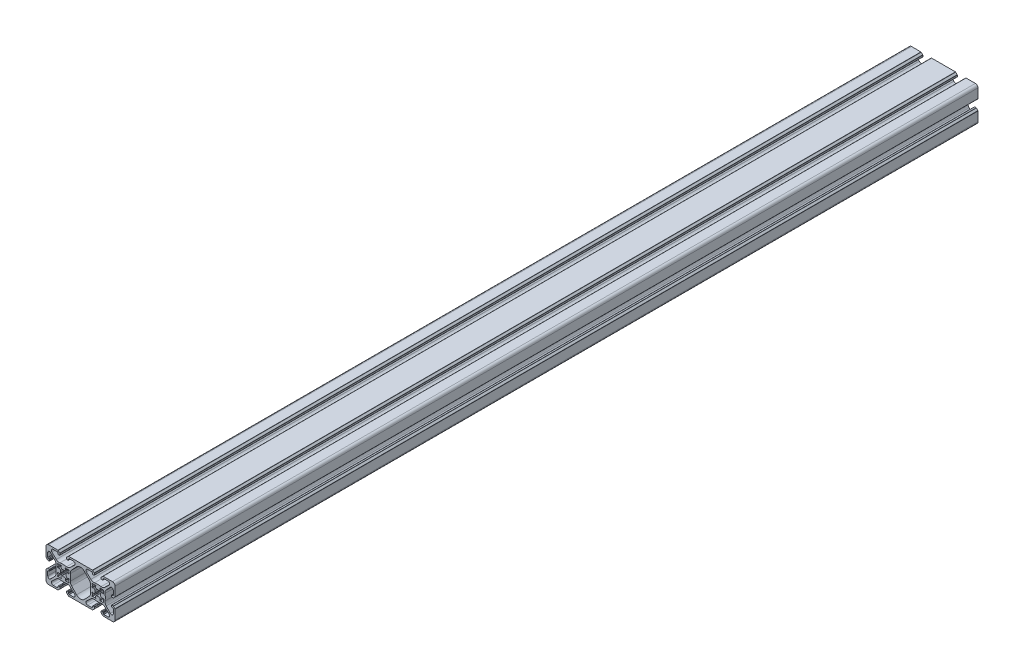
SolidWorks part; units mm, degrees
ref_plane "Front Plane" through (0, 0, 0) normal (0, 0, 1) x (1, 0, 0)
ref_plane "Top Plane" through (0, 0, 0) normal (0, 1, 0) x (1, 0, 0)
ref_plane "Right Plane" through (0, 0, 0) normal (1, 0, 0) x (0, 0, -1)
sketch "Model" plane through (0, 0, 0) normal (0, 0, 1) x (1, 0, 0)
  line L0 (1975.9541, 1652.1362) -> (1976.9672, 1652.4076)
  line L1 (1973.0632, 1648.5036) -> (1973.3346, 1649.5167)
  line L2 (1968.2453, 1649.5167) -> (1968.5168, 1648.5036)
  line L3 (1964.6128, 1652.4076) -> (1965.6258, 1652.1362)
  line L4 (1965.6258, 1657.2255) -> (1964.6128, 1656.954)
  line L5 (1968.5168, 1660.858) -> (1968.2453, 1659.845)
  line L6 (1973.3346, 1659.845) -> (1973.0632, 1660.858)
  line L7 (1976.9672, 1656.954) -> (1975.9541, 1657.2255)
  line L9 (2005.6258, 1652.1362) -> (2004.6128, 1652.4076)
  line L10 (2008.5168, 1648.5036) -> (2008.2453, 1649.5167)
  line L11 (2013.3346, 1649.5167) -> (2013.0632, 1648.5036)
  line L12 (2016.9672, 1652.4076) -> (2015.9541, 1652.1362)
  line L13 (2015.9541, 1657.2255) -> (2016.9672, 1656.954)
  line L14 (2013.0632, 1660.858) -> (2013.3346, 1659.845)
  line L15 (2008.2453, 1659.845) -> (2008.5168, 1660.858)
  line L16 (2004.6128, 1656.954) -> (2005.6258, 1657.2255)
  line L17 (1980.5086, 1646.6346) -> (1986.1807, 1640.6604)
  line L18 (1995.3992, 1640.6604) -> (2001.0713, 1646.6346)
  line L19 (2001.0713, 1662.727) -> (1995.3992, 1668.7012)
  line L20 (1986.1807, 1668.7012) -> (1980.5086, 1662.727)
  line L22 (2004.5828, 1674.6808) -> (1976.9971, 1674.6808)
  line L23 (1976.6435, 1674.5344) -> (1974.9364, 1672.8273)
  line L24 (1974.79, 1672.4737) -> (1974.79, 1670.8808)
  line L25 (1975.29, 1670.3808) -> (1976.29, 1670.3808)
  line L26 (1976.79, 1670.8808) -> (1976.79, 1671.7281)
  line L27 (1976.8778, 1671.9403) -> (1977.5305, 1672.593)
  line L28 (1977.7426, 1672.6808) -> (1982.5473, 1672.6808)
  line L29 (1983.9244, 1669.2304) -> (1978.8362, 1664.3995)
  line L30 (1962.7437, 1664.3995) -> (1957.6555, 1669.2304)
  line L31 (1959.0326, 1672.6808) -> (1963.8373, 1672.6808)
  line L32 (1964.0494, 1672.593) -> (1964.7021, 1671.9403)
  line L33 (1964.79, 1671.7281) -> (1964.79, 1670.8808)
  line L34 (1965.29, 1670.3808) -> (1966.29, 1670.3808)
  line L35 (1966.79, 1670.8808) -> (1966.79, 1672.4737)
  line L36 (1966.6435, 1672.8273) -> (1964.9364, 1674.5344)
  line L37 (1964.5828, 1674.6808) -> (1953.79, 1674.6808)
  line L38 (1950.79, 1671.6808) -> (1950.79, 1660.8879)
  line L39 (1950.9364, 1660.5344) -> (1952.6435, 1658.8273)
  line L40 (1952.9971, 1658.6808) -> (1954.59, 1658.6808)
  line L41 (1955.09, 1659.1808) -> (1955.09, 1660.1808)
  line L42 (1954.59, 1660.6808) -> (1953.7426, 1660.6808)
  line L43 (1953.5305, 1660.7687) -> (1952.8778, 1661.4214)
  line L44 (1952.79, 1661.6335) -> (1952.79, 1666.4382)
  line L45 (1956.2404, 1667.8153) -> (1961.0713, 1662.727)
  line L46 (1961.0713, 1646.6346) -> (1956.2404, 1641.5464)
  line L47 (1952.79, 1642.9235) -> (1952.79, 1647.7281)
  line L48 (1952.8778, 1647.9403) -> (1953.5305, 1648.593)
  line L49 (1953.7426, 1648.6808) -> (1954.59, 1648.6808)
  line L50 (1955.09, 1649.1808) -> (1955.09, 1650.1808)
  line L51 (1954.59, 1650.6808) -> (1952.9971, 1650.6808)
  line L52 (1952.6435, 1650.5344) -> (1950.9364, 1648.8273)
  line L53 (1950.79, 1648.4737) -> (1950.79, 1637.6808)
  line L54 (1953.79, 1634.6808) -> (1964.5828, 1634.6808)
  line L55 (1964.9364, 1634.8273) -> (1966.6435, 1636.5344)
  line L56 (1966.79, 1636.8879) -> (1966.79, 1638.4808)
  line L57 (1966.29, 1638.9808) -> (1965.29, 1638.9808)
  line L58 (1964.79, 1638.4808) -> (1964.79, 1637.6335)
  line L59 (1964.7021, 1637.4214) -> (1964.0494, 1636.7687)
  line L60 (1963.8373, 1636.6808) -> (1959.0326, 1636.6808)
  line L61 (1957.6555, 1640.1312) -> (1962.7437, 1644.9622)
  line L62 (1978.8362, 1644.9622) -> (1983.9244, 1640.1312)
  line L63 (1982.5473, 1636.6808) -> (1977.7426, 1636.6808)
  line L64 (1977.5305, 1636.7687) -> (1976.8778, 1637.4214)
  line L65 (1976.79, 1637.6335) -> (1976.79, 1638.4808)
  line L66 (1976.29, 1638.9808) -> (1975.29, 1638.9808)
  line L67 (1974.79, 1638.4808) -> (1974.79, 1636.8879)
  line L68 (1974.9364, 1636.5344) -> (1976.6435, 1634.8273)
  line L69 (1976.9971, 1634.6808) -> (2004.5828, 1634.6808)
  line L70 (2004.9364, 1634.8273) -> (2006.6435, 1636.5344)
  line L71 (2006.79, 1636.8879) -> (2006.79, 1638.4808)
  line L72 (2006.29, 1638.9808) -> (2005.29, 1638.9808)
  line L73 (2004.79, 1638.4808) -> (2004.79, 1637.6335)
  line L74 (2004.7021, 1637.4214) -> (2004.0494, 1636.7687)
  line L75 (2003.8373, 1636.6808) -> (1999.0326, 1636.6808)
  line L76 (1997.6555, 1640.1312) -> (2002.7437, 1644.9622)
  line L77 (2018.8362, 1644.9622) -> (2023.9244, 1640.1312)
  line L78 (2022.5473, 1636.6808) -> (2017.7426, 1636.6808)
  line L79 (2017.5305, 1636.7687) -> (2016.8778, 1637.4214)
  line L80 (2016.79, 1637.6335) -> (2016.79, 1638.4808)
  line L81 (2016.29, 1638.9808) -> (2015.29, 1638.9808)
  line L82 (2014.79, 1638.4808) -> (2014.79, 1636.8879)
  line L83 (2014.9364, 1636.5344) -> (2016.6435, 1634.8273)
  line L84 (2016.9971, 1634.6808) -> (2027.79, 1634.6808)
  line L85 (2030.79, 1637.6808) -> (2030.79, 1648.4737)
  line L86 (2030.6435, 1648.8273) -> (2028.9364, 1650.5344)
  line L87 (2028.5828, 1650.6808) -> (2026.99, 1650.6808)
  line L88 (2026.49, 1650.1808) -> (2026.49, 1649.1808)
  line L89 (2026.99, 1648.6808) -> (2027.8373, 1648.6808)
  line L90 (2028.0494, 1648.593) -> (2028.7021, 1647.9403)
  line L91 (2028.79, 1647.7281) -> (2028.79, 1642.9235)
  line L92 (2025.3395, 1641.5464) -> (2020.5086, 1646.6346)
  line L93 (2020.5086, 1662.727) -> (2025.3395, 1667.8153)
  line L94 (2028.79, 1666.4382) -> (2028.79, 1661.6335)
  line L95 (2028.7021, 1661.4214) -> (2028.0494, 1660.7687)
  line L96 (2027.8373, 1660.6808) -> (2026.99, 1660.6808)
  line L97 (2026.49, 1660.1808) -> (2026.49, 1659.1808)
  line L98 (2026.99, 1658.6808) -> (2028.5828, 1658.6808)
  line L99 (2028.9364, 1658.8273) -> (2030.6435, 1660.5344)
  line L100 (2030.79, 1660.8879) -> (2030.79, 1671.6808)
  line L101 (2027.79, 1674.6808) -> (2016.9971, 1674.6808)
  line L102 (2016.6435, 1674.5344) -> (2014.9364, 1672.8273)
  line L103 (2014.79, 1672.4737) -> (2014.79, 1670.8808)
  line L104 (2015.29, 1670.3808) -> (2016.29, 1670.3808)
  line L105 (2016.79, 1670.8808) -> (2016.79, 1671.7281)
  line L106 (2016.8778, 1671.9403) -> (2017.5305, 1672.593)
  line L107 (2017.7426, 1672.6808) -> (2022.5473, 1672.6808)
  line L108 (2023.9244, 1669.2304) -> (2018.8362, 1664.3995)
  line L109 (2002.7437, 1664.3995) -> (1997.6555, 1669.2304)
  line L110 (1999.0326, 1672.6808) -> (2003.8373, 1672.6808)
  line L111 (2004.0494, 1672.593) -> (2004.7021, 1671.9403)
  line L112 (2004.79, 1671.7281) -> (2004.79, 1670.8808)
  line L113 (2005.29, 1670.3808) -> (2006.29, 1670.3808)
  line L114 (2006.79, 1670.8808) -> (2006.79, 1672.4737)
  line L115 (2006.6435, 1672.8273) -> (2004.9364, 1674.5344)
  arc A0 (1977.3429, 1652.084) -> (1976.9672, 1652.4076) centre (1977.0448, 1652.1178) ccw
  arc A1 (1977.215, 1651.1353) -> (1977.3429, 1652.084) centre (1954.49, 1654.6808) ccw
  arc A2 (1977.215, 1651.1353) -> (1977.3, 1648.529) centre (1984.1314, 1650.0562) ccw
  arc A3 (1976.9418, 1648.1708) -> (1977.3, 1648.529) centre (1977.0072, 1648.4635) ccw
  arc A4 (1976.9418, 1648.1708) -> (1974.3355, 1648.2557) centre (1975.4145, 1641.3394) ccw
  arc A5 (1973.3868, 1648.1279) -> (1974.3355, 1648.2557) centre (1970.79, 1670.9808) ccw
  arc A6 (1973.0632, 1648.5036) -> (1973.3868, 1648.1279) centre (1973.3529, 1648.426) ccw
  arc A7 (1973.3346, 1649.5167) -> (1971.5503, 1651.3669) centre (1971.8857, 1649.9049) ccw
  arc A8 (1970.0296, 1651.3669) -> (1971.5503, 1651.3669) centre (1970.79, 1654.6808) ccw
  arc A9 (1970.0296, 1651.3669) -> (1968.2453, 1649.5167) centre (1969.6942, 1649.9049) ccw
  arc A10 (1968.1931, 1648.1279) -> (1968.5168, 1648.5036) centre (1968.227, 1648.426) ccw
  arc A11 (1967.2444, 1648.2557) -> (1968.1931, 1648.1279) centre (1970.79, 1670.9808) ccw
  arc A12 (1967.2444, 1648.2557) -> (1964.6381, 1648.1708) centre (1966.1654, 1641.3394) ccw
  arc A13 (1964.2799, 1648.529) -> (1964.6381, 1648.1708) centre (1964.5727, 1648.4635) ccw
  arc A14 (1964.2799, 1648.529) -> (1964.3649, 1651.1353) centre (1957.4485, 1650.0562) ccw
  arc A15 (1964.237, 1652.084) -> (1964.3649, 1651.1353) centre (1987.09, 1654.6808) ccw
  arc A16 (1964.6128, 1652.4076) -> (1964.237, 1652.084) centre (1964.5351, 1652.1178) ccw
  arc A17 (1965.6258, 1652.1362) -> (1967.4761, 1653.9205) centre (1966.014, 1653.5851) ccw
  arc A18 (1967.4761, 1655.4411) -> (1967.4761, 1653.9205) centre (1970.79, 1654.6808) ccw
  arc A19 (1967.4761, 1655.4411) -> (1965.6258, 1657.2255) centre (1966.014, 1655.7766) ccw
  arc A20 (1964.237, 1657.2777) -> (1964.6128, 1656.954) centre (1964.5351, 1657.2438) ccw
  arc A21 (1964.3649, 1658.2263) -> (1964.237, 1657.2777) centre (1987.09, 1654.6808) ccw
  arc A22 (1964.3649, 1658.2263) -> (1964.2799, 1660.8326) centre (1957.4485, 1659.3054) ccw
  arc A23 (1964.6381, 1661.1909) -> (1964.2799, 1660.8326) centre (1964.5727, 1660.8981) ccw
  arc A24 (1964.6381, 1661.1909) -> (1967.2444, 1661.1059) centre (1966.1654, 1668.0222) ccw
  arc A25 (1968.1931, 1661.2338) -> (1967.2444, 1661.1059) centre (1970.79, 1638.3808) ccw
  arc A26 (1968.5168, 1660.858) -> (1968.1931, 1661.2338) centre (1968.227, 1660.9357) ccw
  arc A27 (1968.2453, 1659.845) -> (1970.0296, 1657.9947) centre (1969.6942, 1659.4567) ccw
  arc A28 (1971.5503, 1657.9947) -> (1970.0296, 1657.9947) centre (1970.79, 1654.6808) ccw
  arc A29 (1971.5503, 1657.9947) -> (1973.3346, 1659.845) centre (1971.8857, 1659.4567) ccw
  arc A30 (1973.3868, 1661.2338) -> (1973.0632, 1660.858) centre (1973.3529, 1660.9357) ccw
  arc A31 (1974.3355, 1661.1059) -> (1973.3868, 1661.2338) centre (1970.79, 1638.3808) ccw
  arc A32 (1974.3355, 1661.1059) -> (1976.9418, 1661.1909) centre (1975.4145, 1668.0222) ccw
  arc A33 (1977.3, 1660.8326) -> (1976.9418, 1661.1909) centre (1977.0072, 1660.8981) ccw
  arc A34 (1977.3, 1660.8326) -> (1977.215, 1658.2263) centre (1984.1314, 1659.3054) ccw
  arc A35 (1977.3429, 1657.2777) -> (1977.215, 1658.2263) centre (1954.49, 1654.6808) ccw
  arc A36 (1976.9672, 1656.954) -> (1977.3429, 1657.2777) centre (1977.0448, 1657.2438) ccw
  arc A37 (1975.9541, 1657.2255) -> (1974.1039, 1655.4411) centre (1975.5659, 1655.7766) ccw
  arc A38 (1974.1039, 1653.9205) -> (1974.1039, 1655.4411) centre (1970.79, 1654.6808) ccw
  arc A39 (1974.1039, 1653.9205) -> (1975.9541, 1652.1362) centre (1975.5659, 1653.5851) ccw
  arc A40 (2004.6128, 1652.4076) -> (2004.237, 1652.084) centre (2004.5351, 1652.1178) ccw
  arc A41 (2004.237, 1652.084) -> (2004.3649, 1651.1353) centre (2027.09, 1654.6808) ccw
  arc A42 (2004.2799, 1648.529) -> (2004.3649, 1651.1353) centre (1997.4485, 1650.0562) ccw
  arc A43 (2004.2799, 1648.529) -> (2004.6381, 1648.1708) centre (2004.5727, 1648.4635) ccw
  arc A44 (2007.2444, 1648.2557) -> (2004.6381, 1648.1708) centre (2006.1654, 1641.3394) ccw
  arc A45 (2007.2444, 1648.2557) -> (2008.1931, 1648.1279) centre (2010.79, 1670.9808) ccw
  arc A46 (2008.1931, 1648.1279) -> (2008.5168, 1648.5036) centre (2008.227, 1648.426) ccw
  arc A47 (2010.0296, 1651.3669) -> (2008.2453, 1649.5167) centre (2009.6942, 1649.9049) ccw
  arc A48 (2010.0296, 1651.3669) -> (2011.5503, 1651.3669) centre (2010.79, 1654.6808) ccw
  arc A49 (2013.3346, 1649.5167) -> (2011.5503, 1651.3669) centre (2011.8857, 1649.9049) ccw
  arc A50 (2013.0632, 1648.5036) -> (2013.3868, 1648.1279) centre (2013.3529, 1648.426) ccw
  arc A51 (2013.3868, 1648.1279) -> (2014.3355, 1648.2557) centre (2010.79, 1670.9808) ccw
  arc A52 (2016.9418, 1648.1708) -> (2014.3355, 1648.2557) centre (2015.4145, 1641.3394) ccw
  arc A53 (2016.9418, 1648.1708) -> (2017.3, 1648.529) centre (2017.0072, 1648.4635) ccw
  arc A54 (2017.215, 1651.1353) -> (2017.3, 1648.529) centre (2024.1314, 1650.0562) ccw
  arc A55 (2017.215, 1651.1353) -> (2017.3429, 1652.084) centre (1994.49, 1654.6808) ccw
  arc A56 (2017.3429, 1652.084) -> (2016.9672, 1652.4076) centre (2017.0448, 1652.1178) ccw
  arc A57 (2014.1039, 1653.9205) -> (2015.9541, 1652.1362) centre (2015.5659, 1653.5851) ccw
  arc A58 (2014.1039, 1653.9205) -> (2014.1039, 1655.4411) centre (2010.79, 1654.6808) ccw
  arc A59 (2015.9541, 1657.2255) -> (2014.1039, 1655.4411) centre (2015.5659, 1655.7766) ccw
  arc A60 (2016.9672, 1656.954) -> (2017.3429, 1657.2777) centre (2017.0448, 1657.2438) ccw
  arc A61 (2017.3429, 1657.2777) -> (2017.215, 1658.2263) centre (1994.49, 1654.6808) ccw
  arc A62 (2017.3, 1660.8326) -> (2017.215, 1658.2263) centre (2024.1314, 1659.3054) ccw
  arc A63 (2017.3, 1660.8326) -> (2016.9418, 1661.1909) centre (2017.0072, 1660.8981) ccw
  arc A64 (2014.3355, 1661.1059) -> (2016.9418, 1661.1909) centre (2015.4145, 1668.0222) ccw
  arc A65 (2014.3355, 1661.1059) -> (2013.3868, 1661.2338) centre (2010.79, 1638.3808) ccw
  arc A66 (2013.3868, 1661.2338) -> (2013.0632, 1660.858) centre (2013.3529, 1660.9357) ccw
  arc A67 (2011.5503, 1657.9947) -> (2013.3346, 1659.845) centre (2011.8857, 1659.4567) ccw
  arc A68 (2011.5503, 1657.9947) -> (2010.0296, 1657.9947) centre (2010.79, 1654.6808) ccw
  arc A69 (2008.2453, 1659.845) -> (2010.0296, 1657.9947) centre (2009.6942, 1659.4567) ccw
  arc A70 (2008.5168, 1660.858) -> (2008.1931, 1661.2338) centre (2008.227, 1660.9357) ccw
  arc A71 (2008.1931, 1661.2338) -> (2007.2444, 1661.1059) centre (2010.79, 1638.3808) ccw
  arc A72 (2004.6381, 1661.1909) -> (2007.2444, 1661.1059) centre (2006.1654, 1668.0222) ccw
  arc A73 (2004.6381, 1661.1909) -> (2004.2799, 1660.8326) centre (2004.5727, 1660.8981) ccw
  arc A74 (2004.3649, 1658.2263) -> (2004.2799, 1660.8326) centre (1997.4485, 1659.3054) ccw
  arc A75 (2004.3649, 1658.2263) -> (2004.237, 1657.2777) centre (2027.09, 1654.6808) ccw
  arc A76 (2004.237, 1657.2777) -> (2004.6128, 1656.954) centre (2004.5351, 1657.2438) ccw
  arc A77 (2007.4761, 1655.4411) -> (2005.6258, 1657.2255) centre (2006.014, 1655.7766) ccw
  arc A78 (2007.4761, 1655.4411) -> (2007.4761, 1653.9205) centre (2010.79, 1654.6808) ccw
  arc A79 (2005.6258, 1652.1362) -> (2007.4761, 1653.9205) centre (2006.014, 1653.5851) ccw
  arc A80 (1979.1939, 1650.8445) -> (1979.1939, 1658.5171) centre (1954.49, 1654.6808) ccw
  arc A81 (1979.1939, 1650.8445) -> (1980.5086, 1646.6346) centre (1984.1346, 1650.0773) ccw
  arc A82 (1986.1807, 1640.6604) -> (1995.3992, 1640.6604) centre (1990.79, 1645.0366) ccw
  arc A83 (2001.0713, 1646.6346) -> (2002.3861, 1650.8445) centre (1997.4453, 1650.0773) ccw
  arc A84 (2002.3861, 1658.5171) -> (2002.3861, 1650.8445) centre (2027.09, 1654.6808) ccw
  arc A85 (2002.3861, 1658.5171) -> (2001.0713, 1662.727) centre (1997.4453, 1659.2844) ccw
  arc A86 (1995.3992, 1668.7012) -> (1986.1807, 1668.7012) centre (1990.79, 1664.325) ccw
  arc A87 (1980.5086, 1662.727) -> (1979.1939, 1658.5171) centre (1984.1346, 1659.2844) ccw
  arc A88 (1976.9971, 1674.6808) -> (1976.6435, 1674.5344) centre (1976.9971, 1674.1808) ccw
  arc A89 (1974.9364, 1672.8273) -> (1974.79, 1672.4737) centre (1975.29, 1672.4737) ccw
  arc A90 (1974.79, 1670.8808) -> (1975.29, 1670.3808) centre (1975.29, 1670.8808) ccw
  arc A91 (1976.29, 1670.3808) -> (1976.79, 1670.8808) centre (1976.29, 1670.8808) ccw
  arc A92 (1976.8778, 1671.9403) -> (1976.79, 1671.7281) centre (1977.09, 1671.7281) ccw
  arc A93 (1977.7426, 1672.6808) -> (1977.5305, 1672.593) centre (1977.7426, 1672.3808) ccw
  arc A94 (1983.9244, 1669.2304) -> (1982.5473, 1672.6808) centre (1982.5473, 1670.6808) ccw
  arc A95 (1974.6262, 1663.0847) -> (1978.8362, 1664.3995) centre (1975.3935, 1668.0255) ccw
  arc A96 (1974.6262, 1663.0847) -> (1966.9537, 1663.0847) centre (1970.79, 1638.3808) ccw
  arc A97 (1962.7437, 1664.3995) -> (1966.9537, 1663.0847) centre (1966.1864, 1668.0255) ccw
  arc A98 (1959.0326, 1672.6808) -> (1957.6555, 1669.2304) centre (1959.0326, 1670.6808) ccw
  arc A99 (1964.0494, 1672.593) -> (1963.8373, 1672.6808) centre (1963.8373, 1672.3808) ccw
  arc A100 (1964.79, 1671.7281) -> (1964.7021, 1671.9403) centre (1964.49, 1671.7281) ccw
  arc A101 (1964.79, 1670.8808) -> (1965.29, 1670.3808) centre (1965.29, 1670.8808) ccw
  arc A102 (1966.29, 1670.3808) -> (1966.79, 1670.8808) centre (1966.29, 1670.8808) ccw
  arc A103 (1966.79, 1672.4737) -> (1966.6435, 1672.8273) centre (1966.29, 1672.4737) ccw
  arc A104 (1964.9364, 1674.5344) -> (1964.5828, 1674.6808) centre (1964.5828, 1674.1808) ccw
  arc A105 (1953.79, 1674.6808) -> (1950.79, 1671.6808) centre (1953.79, 1671.6808) ccw
  arc A106 (1950.79, 1660.8879) -> (1950.9364, 1660.5344) centre (1951.29, 1660.8879) ccw
  arc A107 (1952.6435, 1658.8273) -> (1952.9971, 1658.6808) centre (1952.9971, 1659.1808) ccw
  arc A108 (1954.59, 1658.6808) -> (1955.09, 1659.1808) centre (1954.59, 1659.1808) ccw
  arc A109 (1955.09, 1660.1808) -> (1954.59, 1660.6808) centre (1954.59, 1660.1808) ccw
  arc A110 (1953.5305, 1660.7687) -> (1953.7426, 1660.6808) centre (1953.7426, 1660.9808) ccw
  arc A111 (1952.79, 1661.6335) -> (1952.8778, 1661.4214) centre (1953.09, 1661.6335) ccw
  arc A112 (1956.2404, 1667.8153) -> (1952.79, 1666.4382) centre (1954.79, 1666.4382) ccw
  arc A113 (1962.3861, 1658.5171) -> (1961.0713, 1662.727) centre (1957.4453, 1659.2844) ccw
  arc A114 (1962.3861, 1658.5171) -> (1962.3861, 1650.8445) centre (1987.09, 1654.6808) ccw
  arc A115 (1961.0713, 1646.6346) -> (1962.3861, 1650.8445) centre (1957.4453, 1650.0773) ccw
  arc A116 (1952.79, 1642.9235) -> (1956.2404, 1641.5464) centre (1954.79, 1642.9235) ccw
  arc A117 (1952.8778, 1647.9403) -> (1952.79, 1647.7281) centre (1953.09, 1647.7281) ccw
  arc A118 (1953.7426, 1648.6808) -> (1953.5305, 1648.593) centre (1953.7426, 1648.3808) ccw
  arc A119 (1954.59, 1648.6808) -> (1955.09, 1649.1808) centre (1954.59, 1649.1808) ccw
  arc A120 (1955.09, 1650.1808) -> (1954.59, 1650.6808) centre (1954.59, 1650.1808) ccw
  arc A121 (1952.9971, 1650.6808) -> (1952.6435, 1650.5344) centre (1952.9971, 1650.1808) ccw
  arc A122 (1950.9364, 1648.8273) -> (1950.79, 1648.4737) centre (1951.29, 1648.4737) ccw
  arc A123 (1950.79, 1637.6808) -> (1953.79, 1634.6808) centre (1953.79, 1637.6808) ccw
  arc A124 (1964.5828, 1634.6808) -> (1964.9364, 1634.8273) centre (1964.5828, 1635.1808) ccw
  arc A125 (1966.6435, 1636.5344) -> (1966.79, 1636.8879) centre (1966.29, 1636.8879) ccw
  arc A126 (1966.79, 1638.4808) -> (1966.29, 1638.9808) centre (1966.29, 1638.4808) ccw
  arc A127 (1965.29, 1638.9808) -> (1964.79, 1638.4808) centre (1965.29, 1638.4808) ccw
  arc A128 (1964.7021, 1637.4214) -> (1964.79, 1637.6335) centre (1964.49, 1637.6335) ccw
  arc A129 (1963.8373, 1636.6808) -> (1964.0494, 1636.7687) centre (1963.8373, 1636.9808) ccw
  arc A130 (1957.6555, 1640.1312) -> (1959.0326, 1636.6808) centre (1959.0326, 1638.6808) ccw
  arc A131 (1966.9537, 1646.2769) -> (1962.7437, 1644.9622) centre (1966.1864, 1641.3361) ccw
  arc A132 (1966.9537, 1646.2769) -> (1974.6262, 1646.2769) centre (1970.79, 1670.9808) ccw
  arc A133 (1978.8362, 1644.9622) -> (1974.6262, 1646.2769) centre (1975.3935, 1641.3361) ccw
  arc A134 (1982.5473, 1636.6808) -> (1983.9244, 1640.1312) centre (1982.5473, 1638.6808) ccw
  arc A135 (1977.5305, 1636.7687) -> (1977.7426, 1636.6808) centre (1977.7426, 1636.9808) ccw
  arc A136 (1976.79, 1637.6335) -> (1976.8778, 1637.4214) centre (1977.09, 1637.6335) ccw
  arc A137 (1976.79, 1638.4808) -> (1976.29, 1638.9808) centre (1976.29, 1638.4808) ccw
  arc A138 (1975.29, 1638.9808) -> (1974.79, 1638.4808) centre (1975.29, 1638.4808) ccw
  arc A139 (1974.79, 1636.8879) -> (1974.9364, 1636.5344) centre (1975.29, 1636.8879) ccw
  arc A140 (1976.6435, 1634.8273) -> (1976.9971, 1634.6808) centre (1976.9971, 1635.1808) ccw
  arc A141 (2004.5828, 1634.6808) -> (2004.9364, 1634.8273) centre (2004.5828, 1635.1808) ccw
  arc A142 (2006.6435, 1636.5344) -> (2006.79, 1636.8879) centre (2006.29, 1636.8879) ccw
  arc A143 (2006.79, 1638.4808) -> (2006.29, 1638.9808) centre (2006.29, 1638.4808) ccw
  arc A144 (2005.29, 1638.9808) -> (2004.79, 1638.4808) centre (2005.29, 1638.4808) ccw
  arc A145 (2004.7021, 1637.4214) -> (2004.79, 1637.6335) centre (2004.49, 1637.6335) ccw
  arc A146 (2003.8373, 1636.6808) -> (2004.0494, 1636.7687) centre (2003.8373, 1636.9808) ccw
  arc A147 (1997.6555, 1640.1312) -> (1999.0326, 1636.6808) centre (1999.0326, 1638.6808) ccw
  arc A148 (2006.9537, 1646.2769) -> (2002.7437, 1644.9622) centre (2006.1864, 1641.3361) ccw
  arc A149 (2006.9537, 1646.2769) -> (2014.6262, 1646.2769) centre (2010.79, 1670.9808) ccw
  arc A150 (2018.8362, 1644.9622) -> (2014.6262, 1646.2769) centre (2015.3935, 1641.3361) ccw
  arc A151 (2022.5473, 1636.6808) -> (2023.9244, 1640.1312) centre (2022.5473, 1638.6808) ccw
  arc A152 (2017.5305, 1636.7687) -> (2017.7426, 1636.6808) centre (2017.7426, 1636.9808) ccw
  arc A153 (2016.79, 1637.6335) -> (2016.8778, 1637.4214) centre (2017.09, 1637.6335) ccw
  arc A154 (2016.79, 1638.4808) -> (2016.29, 1638.9808) centre (2016.29, 1638.4808) ccw
  arc A155 (2015.29, 1638.9808) -> (2014.79, 1638.4808) centre (2015.29, 1638.4808) ccw
  arc A156 (2014.79, 1636.8879) -> (2014.9364, 1636.5344) centre (2015.29, 1636.8879) ccw
  arc A157 (2016.6435, 1634.8273) -> (2016.9971, 1634.6808) centre (2016.9971, 1635.1808) ccw
  arc A158 (2027.79, 1634.6808) -> (2030.79, 1637.6808) centre (2027.79, 1637.6808) ccw
  arc A159 (2030.79, 1648.4737) -> (2030.6435, 1648.8273) centre (2030.29, 1648.4737) ccw
  arc A160 (2028.9364, 1650.5344) -> (2028.5828, 1650.6808) centre (2028.5828, 1650.1808) ccw
  arc A161 (2026.99, 1650.6808) -> (2026.49, 1650.1808) centre (2026.99, 1650.1808) ccw
  arc A162 (2026.49, 1649.1808) -> (2026.99, 1648.6808) centre (2026.99, 1649.1808) ccw
  arc A163 (2028.0494, 1648.593) -> (2027.8373, 1648.6808) centre (2027.8373, 1648.3808) ccw
  arc A164 (2028.79, 1647.7281) -> (2028.7021, 1647.9403) centre (2028.49, 1647.7281) ccw
  arc A165 (2025.3395, 1641.5464) -> (2028.79, 1642.9235) centre (2026.79, 1642.9235) ccw
  arc A166 (2019.1939, 1650.8445) -> (2020.5086, 1646.6346) centre (2024.1346, 1650.0773) ccw
  arc A167 (2019.1939, 1650.8445) -> (2019.1939, 1658.5171) centre (1994.49, 1654.6808) ccw
  arc A168 (2020.5086, 1662.727) -> (2019.1939, 1658.5171) centre (2024.1346, 1659.2844) ccw
  arc A169 (2028.79, 1666.4382) -> (2025.3395, 1667.8153) centre (2026.79, 1666.4382) ccw
  arc A170 (2028.7021, 1661.4214) -> (2028.79, 1661.6335) centre (2028.49, 1661.6335) ccw
  arc A171 (2027.8373, 1660.6808) -> (2028.0494, 1660.7687) centre (2027.8373, 1660.9808) ccw
  arc A172 (2026.99, 1660.6808) -> (2026.49, 1660.1808) centre (2026.99, 1660.1808) ccw
  arc A173 (2026.49, 1659.1808) -> (2026.99, 1658.6808) centre (2026.99, 1659.1808) ccw
  arc A174 (2028.5828, 1658.6808) -> (2028.9364, 1658.8273) centre (2028.5828, 1659.1808) ccw
  arc A175 (2030.6435, 1660.5344) -> (2030.79, 1660.8879) centre (2030.29, 1660.8879) ccw
  arc A176 (2030.79, 1671.6808) -> (2027.79, 1674.6808) centre (2027.79, 1671.6808) ccw
  arc A177 (2016.9971, 1674.6808) -> (2016.6435, 1674.5344) centre (2016.9971, 1674.1808) ccw
  arc A178 (2014.9364, 1672.8273) -> (2014.79, 1672.4737) centre (2015.29, 1672.4737) ccw
  arc A179 (2014.79, 1670.8808) -> (2015.29, 1670.3808) centre (2015.29, 1670.8808) ccw
  arc A180 (2016.29, 1670.3808) -> (2016.79, 1670.8808) centre (2016.29, 1670.8808) ccw
  arc A181 (2016.8778, 1671.9403) -> (2016.79, 1671.7281) centre (2017.09, 1671.7281) ccw
  arc A182 (2017.7426, 1672.6808) -> (2017.5305, 1672.593) centre (2017.7426, 1672.3808) ccw
  arc A183 (2023.9244, 1669.2304) -> (2022.5473, 1672.6808) centre (2022.5473, 1670.6808) ccw
  arc A184 (2014.6262, 1663.0847) -> (2018.8362, 1664.3995) centre (2015.3935, 1668.0255) ccw
  arc A185 (2014.6262, 1663.0847) -> (2006.9537, 1663.0847) centre (2010.79, 1638.3808) ccw
  arc A186 (2002.7437, 1664.3995) -> (2006.9537, 1663.0847) centre (2006.1864, 1668.0255) ccw
  arc A187 (1999.0326, 1672.6808) -> (1997.6555, 1669.2304) centre (1999.0326, 1670.6808) ccw
  arc A188 (2004.0494, 1672.593) -> (2003.8373, 1672.6808) centre (2003.8373, 1672.3808) ccw
  arc A189 (2004.79, 1671.7281) -> (2004.7021, 1671.9403) centre (2004.49, 1671.7281) ccw
  arc A190 (2004.79, 1670.8808) -> (2005.29, 1670.3808) centre (2005.29, 1670.8808) ccw
  arc A191 (2006.29, 1670.3808) -> (2006.79, 1670.8808) centre (2006.29, 1670.8808) ccw
  arc A192 (2006.79, 1672.4737) -> (2006.6435, 1672.8273) centre (2006.29, 1672.4737) ccw
  arc A193 (2004.9364, 1674.5344) -> (2004.5828, 1674.6808) centre (2004.5828, 1674.1808) ccw
  point P480 (0, 0)
  point P481 (0, 0)
  point P482 (0, 0)
  point P483 (0, 0)
  point P484 (0, 0)
  dimension "D2" = 3
  dimension "D1" = 10.7929
extrude "Boss-Extrude1" add sketch "Model" along normal blind 1000
